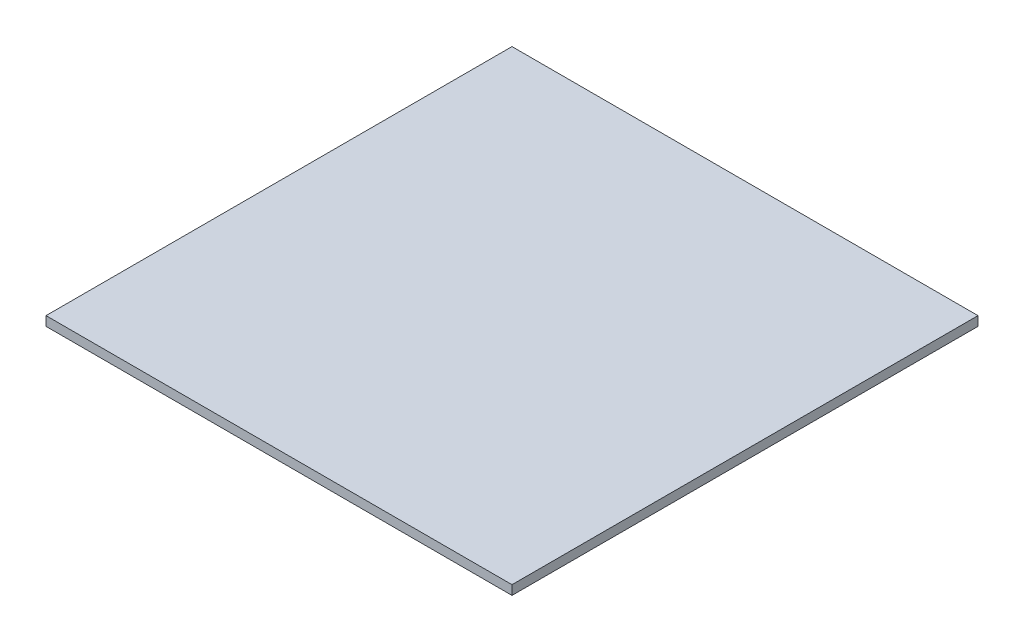
SolidWorks part; units mm, degrees
ref_plane "Face" through (0, 0, 0) normal (0, 0, 1) x (1, 0, 0)
ref_plane "Dessus" through (0, 0, 0) normal (0, 1, 0) x (1, 0, 0)
ref_plane "Droite" through (0, 0, 0) normal (1, 0, 0) x (0, 0, -1)
sketch "Esquisse1" plane through (0, 0, 0) normal (0, 1, 0) x (1, 0, 0)
  line L1 (0, 0) -> (500, 0)
  line L2 (0, 0) -> (0, 500)
  line L3 (0, 500) -> (500, 500)
  line L4 (500, 0) -> (500, 500)
  dimension "D1" = 500
extrude "Extrusion1" add sketch "Esquisse1" along normal blind 10
